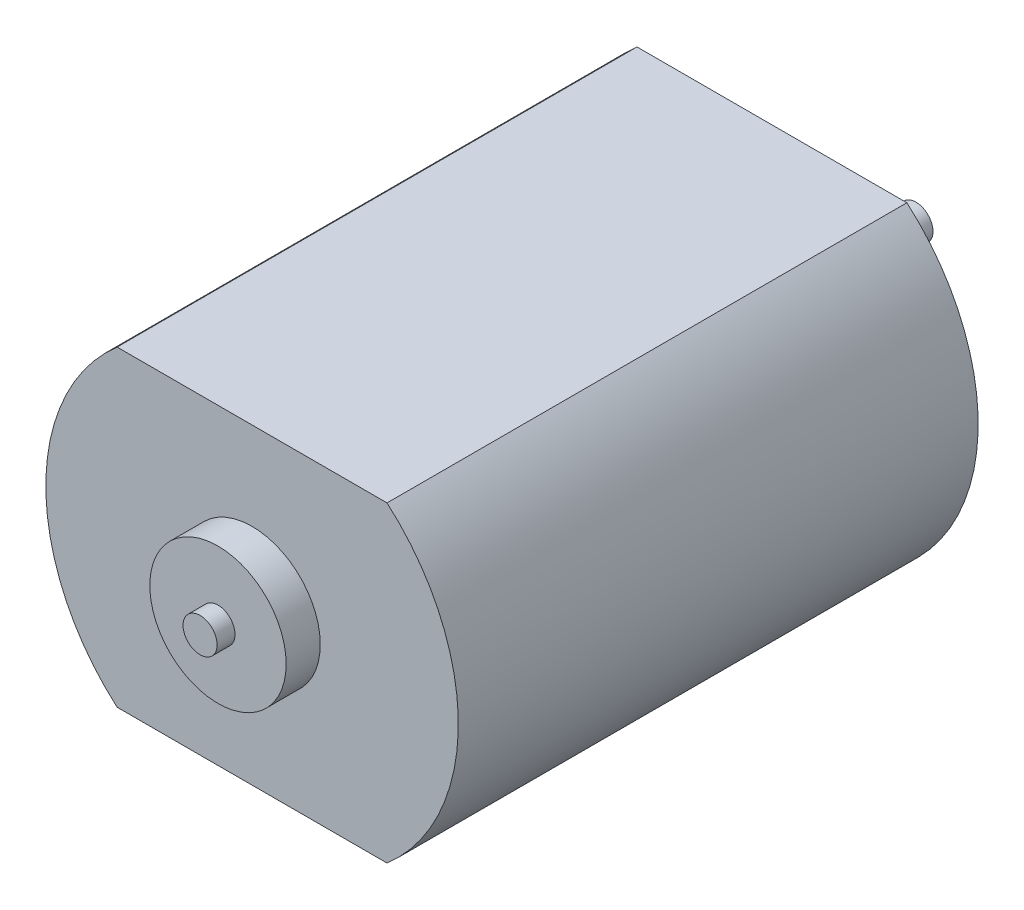
SolidWorks part; units mm, degrees
material "ABS"
ref_plane "Front" through (0, 0, 0) normal (0, 0, 1) x (1, 0, 0)
ref_plane "Top" through (0, 0, 0) normal (0, 1, 0) x (1, 0, 0)
ref_plane "Right" through (0, 0, 0) normal (1, 0, 0) x (0, 0, -1)
sketch "Sketch1" plane through (0, 0, 0) normal (0, 0, 1) x (1, 0, 0)
  line L1 (-7.9175, 9.15) -> (7.9175, 9.15)
  line L2 (-7.9175, 9.15) -> (-7.9175, -9.15) construction
  line L3 (-7.9175, -9.15) -> (7.9175, -9.15)
  line L4 (7.9175, 9.15) -> (7.9175, -9.15) construction
  line L5 (-7.9175, 9.15) -> (7.9175, -9.15) construction
  line L6 (-7.9175, -9.15) -> (7.9175, 9.15) construction
  arc A0 (-7.9175, 9.15) -> (-7.9175, -9.15) centre (0, 0) ccw
  arc A1 (7.9175, -9.15) -> (7.9175, 9.15) centre (0, 0) ccw
  point P0 (0, 0)
  dimension "D1" = 24.2
  dimension "D2" = 18.3
extrude "Boss-Extrude1" add sketch "Sketch1" along normal blind 30.5
sketch "Sketch2" plane through (0, 0, 0) normal (0, 0, -1) x (-1, 0, 0)
  circle A0 centre (0, 0) radius 3.075
  dimension "D1" = 6.15
extrude "Boss-Extrude2" add sketch "Sketch2" along normal blind 1.6
sketch "Sketch3" plane through (0, 0, -1.6) normal (0, 0, -1) x (-1, 0, 0)
  circle A0 centre (0, 0) radius 1
  dimension "D1" = 2
extrude "Boss-Extrude3" add sketch "Sketch3" along normal blind 6.85
sketch "Sketch4" plane through (0, 0, 30.5) normal (0, 0, 1) x (1, 0, 0)
  circle A0 centre (0, 0) radius 4
  dimension "D1" = 8
extrude "Boss-Extrude4" add sketch "Sketch4" along normal blind 2
sketch "Sketch5" plane through (0, 0, 32.5) normal (0, 0, 1) x (1, 0, 0)
  circle A0 centre (0, 0) radius 1
  dimension "D1" = 2
extrude "Boss-Extrude5" add sketch "Sketch5" along normal blind 1.05
